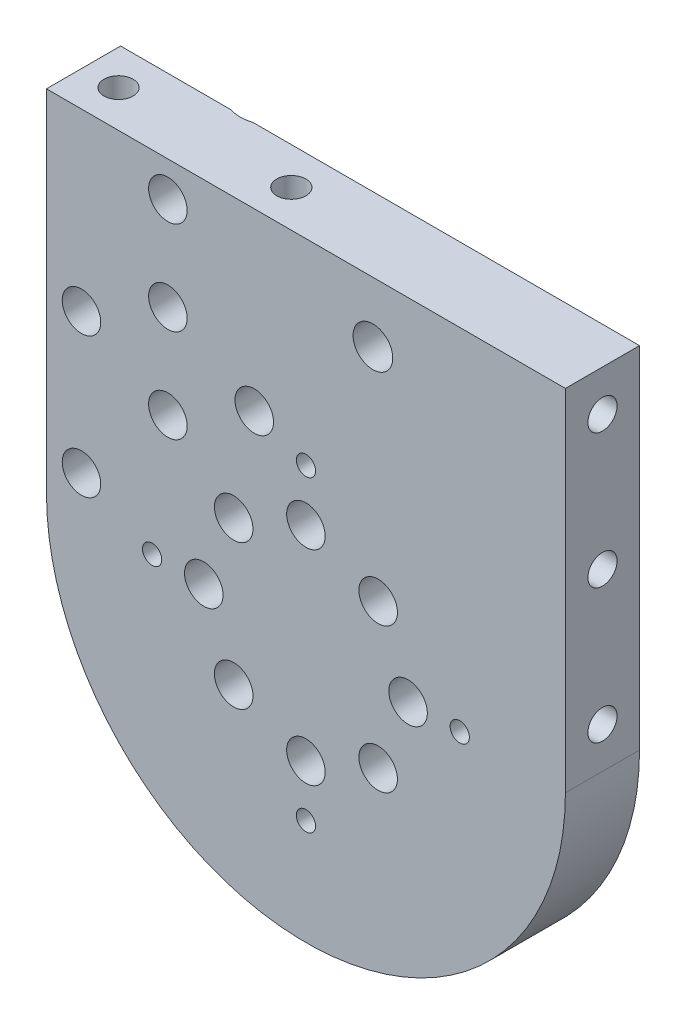
SolidWorks part; units mm, degrees
ref_plane "Front Plane" through (0, 0, 0) normal (0, 0, 1) x (1, 0, 0)
ref_plane "Top Plane" through (0, 0, 0) normal (0, 1, 0) x (1, 0, 0)
ref_plane "Right Plane" through (0, 0, 0) normal (1, 0, 0) x (0, 0, -1)
ref_plane "Plane1" through (0, 0, 0) normal (0, 0, -1) x (-1, 0, 0)
sketch "Sketch1" plane through (0, 0, 0) normal (0, 0, -1) x (-1, 0, 0)
  line L0 (44.45, 0) -> (44.45, 60)
  line L1 (44.45, 60) -> (-44.45, 60)
  line L2 (-44.45, 60) -> (-44.45, 0)
  arc A0 (-44.45, 0) -> (44.45, 0) centre (0, 0) ccw
extrude "Boss-Extrude1" add sketch "Sketch1" against normal blind 12.7
hole_wizard "#4 Clearance Hole1" positions "Sketch3" profile "Sketch2" hole size "#4" standard "ANSI Inch"
sketch "Sketch3" plane through (0, 0, 12.7) normal (0, 0, 1) x (1, 0, 0)
  point P0 (26.35, 0)
  point P1 (0, -26.35)
  point P2 (-26.35, 0)
  point P3 (0, 26.35)
sketch "Sketch2" plane through (26.35, 0, 12.7) normal (1, 0, 0) x (0, -1, 0)
  line L0 (0, 0) -> (0, 12.7)
  line L1 (0, 12.7) -> (1.65, 12.7)
  line L2 (1.65, 12.7) -> (1.65, 0)
  line L5 (1.65, 0) -> (0, 0)
  line L11 (0, -6.35) -> (0, 107.95) construction
  dimension "Thru Hole Dia." = 3.3
  dimension "Thru Hole Depth" = 12.7
hole_wizard "1/4 Clearance Hole1" positions "Sketch5" profile "Sketch4" hole size "1/4" standard "ANSI Inch"
sketch "Sketch5" plane through (0, 0, 0) normal (0, 0, -1) x (-1, 0, 0)
  point P0 (8.85, 30)
  point P1 (23.65, 38)
  point P2 (23.65, 22)
sketch "Sketch4" plane through (-8.85, 30, 0) normal (1, 0, 0) x (0, 1, 0)
  line L0 (0, 0) -> (0, 12.7)
  line L1 (0, 12.7) -> (3.3, 12.7)
  line L2 (3.3, 12.7) -> (3.3, 0)
  line L5 (3.3, 0) -> (0, 0)
  line L11 (0, -6.35) -> (0, 107.95) construction
  dimension "Thru Hole Dia." = 6.6
  dimension "Thru Hole Depth" = 12.7
hole_wizard "1/4 Clearance Hole2" positions "Sketch7" profile "Sketch6" hole size "1/4" standard "ANSI Inch"
sketch "Sketch7" plane through (0, 0, 12.7) normal (0, 0, 1) x (1, 0, 0)
  point P0 (11.4725, 49.6929)
sketch "Sketch6" plane through (11.4725, 49.6929, 12.7) normal (1, 0, 0) x (0, -1, 0)
  line L0 (0, 0) -> (0, 12.7)
  line L1 (0, 12.7) -> (3.4, 12.7)
  line L2 (3.4, 12.7) -> (3.4, 0)
  line L5 (3.4, 0) -> (0, 0)
  line L11 (0, -6.35) -> (0, 107.95) construction
  dimension "Thru Hole Dia." = 6.8
  dimension "Thru Hole Depth" = 12.7
hole_wizard "CSK for 1/4 Flat Head Machine Screw (100)1" positions "Sketch9" profile "Sketch8" countersink size "1/4" standard "ANSI Inch"
sketch "Sketch9" plane through (0, 0, 0) normal (0, 0, -1) x (-1, 0, 0)
  point P0 (23.65, 54)
  point P1 (38.45, 6)
  point P2 (38.45, 30)
sketch "Sketch8" plane through (-23.65, 54, 0) normal (1, 0, 0) x (0, 1, 0)
  line L0 (0, 0) -> (0, 12.7)
  line L1 (0, 12.7) -> (3.3, 12.7)
  line L2 (3.3, 12.7) -> (3.3, 3)
  line L3 (3.3, 3) -> (6.3, 0)
  line L5 (6.3, 0) -> (0, 0)
  line L6 (-3.3, 3) -> (-6.3, 0) construction
  line L11 (0, -6.35) -> (0, 107.95) construction
  dimension "Thru Hole Dia." = 6.6
  dimension "Thru Hole Depth" = 12.7
  dimension "Near C'Sink Dia." = 12.6
  dimension "Near C'Sink Angle" = 90
hole_wizard "#10 Clearance Hole1" positions "Sketch11" profile "Sketch10" hole size "#10" standard "ANSI Inch"
sketch "Sketch11" plane through (0, 60, 0) normal (0, 1, 0) x (1, 0, 0)
  point P0 (-38.45, -6.35)
  point P1 (-8.85, -6.35)
sketch "Sketch10" plane through (-38.45, 60, 6.35) normal (1, 0, 0) x (0, 0, 1)
  line L0 (0, 0) -> (0, 15)
  line L1 (0, 15) -> (2.5, 15)
  line L2 (2.5, 15) -> (2.5, 0)
  line L5 (2.5, 0) -> (0, 0)
  line L10 (0, 15) -> (-2.5, 15) construction
  line L11 (0, -6.35) -> (0, 107.95) construction
  dimension "Hole Dia." = 5
  dimension "Hole Depth" = 15
  dimension "Drill Angle" = 180
hole_wizard "#10 Clearance Hole2" positions "Sketch13" profile "Sketch12" hole size "#10" standard "ANSI Inch"
sketch "Sketch13" plane through (44.45, 0, 0) normal (1, 0, 0) x (0, 0, -1)
  point P0 (-6.35, 7)
  point P1 (-6.35, 53)
  point P2 (-6.35, 30)
sketch "Sketch12" plane through (44.45, 7, 6.35) normal (0, 1, 0) x (0, 0, -1)
  line L0 (0, 0) -> (0, 10)
  line L1 (0, 10) -> (2.5, 10)
  line L2 (2.5, 10) -> (2.5, 0)
  line L5 (2.5, 0) -> (0, 0)
  line L10 (0, 10) -> (-2.5, 10) construction
  line L11 (0, -6.35) -> (0, 107.95) construction
  dimension "Hole Dia." = 5
  dimension "Hole Depth" = 10
  dimension "Drill Angle" = 180
hole_wizard "1-3/4 Clearance Hole1" positions "Sketch15" profile "Sketch14" hole size "1-3/4" standard "ANSI Inch"
sketch "Sketch15" plane through (0, 0, 0) normal (0, 0, -1) x (-1, 0, 0)
  point P0 (0, 0)
sketch "Sketch14" plane through (0, 0, 0) normal (1, 0, 0) x (0, 1, 0)
  line L0 (0, 0) -> (0, 5)
  line L1 (0, 5) -> (22.5, 5)
  line L2 (22.5, 5) -> (22.5, 0)
  line L5 (22.5, 0) -> (0, 0)
  line L10 (0, 5) -> (-22.5, 5) construction
  line L11 (0, -6.35) -> (0, 107.95) construction
  dimension "Hole Dia." = 45
  dimension "Hole Depth" = 5
  dimension "Drill Angle" = 180
hole_wizard "1/4 Clearance Hole3" positions "Sketch17" profile "Sketch16" hole size "1/4" standard "ANSI Inch"
sketch "Sketch17" plane through (0, 0, 12.7) normal (0, 0, 1) x (1, 0, 0)
  point P0 (12.3741, 12.3737)
  point P1 (17.499, -0.001)
  point P2 (12.3727, -12.3751)
  point P3 (-0.002, -17.5)
  point P4 (-12.3761, -12.3737)
  point P5 (-17.501, 0.001)
  point P6 (-12.3747, 12.3751)
  point P7 (0, 17.5)
sketch "Sketch16" plane through (12.3741, 12.3737, 12.7) normal (1, 0, 0) x (0, -1, 0)
  line L0 (0, 0) -> (0, 12.7)
  line L1 (0, 12.7) -> (3.3, 12.7)
  line L2 (3.3, 12.7) -> (3.3, 0)
  line L5 (3.3, 0) -> (0, 0)
  line L11 (0, -6.35) -> (0, 107.95) construction
  dimension "Thru Hole Dia." = 6.6
  dimension "Thru Hole Depth" = 12.7
chamfer "Chamfer1" distance 3 angle 45 3 edges at (-26.95, 38, 0) (-12.15, 30, 0) (-26.95, 22, 0)
